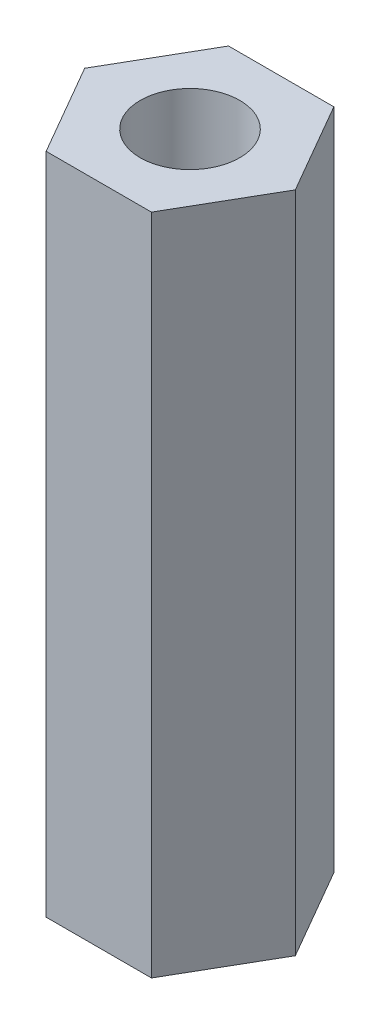
SolidWorks part; units mm, degrees
ref_plane "Front" through (0, 0, 0) normal (0, 0, 1) x (1, 0, 0)
ref_plane "Top" through (0, 0, 0) normal (0, 1, 0) x (1, 0, 0)
ref_plane "Right" through (0, 0, 0) normal (1, 0, 0) x (0, 0, -1)
sketch "Sketch1" plane through (0, 0, 0) normal (0, 1, 0) x (1, 0, 0)
  line L1 (3.1754, 0) -> (1.5877, 2.75)
  line L2 (1.5877, 2.75) -> (-1.5877, 2.75)
  line L3 (-1.5877, 2.75) -> (-3.1754, 0)
  line L4 (-3.1754, 0) -> (-1.5877, -2.75)
  line L5 (-1.5877, -2.75) -> (1.5877, -2.75)
  line L6 (1.5877, -2.75) -> (3.1754, 0)
  circle A0 centre (0, 0) radius 2.75 construction
  circle A1 centre (0, 0) radius 1.5
  dimension "D1" = 5.5
  dimension "D2" = 3
extrude "Boss-Extrude1" add sketch "Sketch1" along normal blind 20
